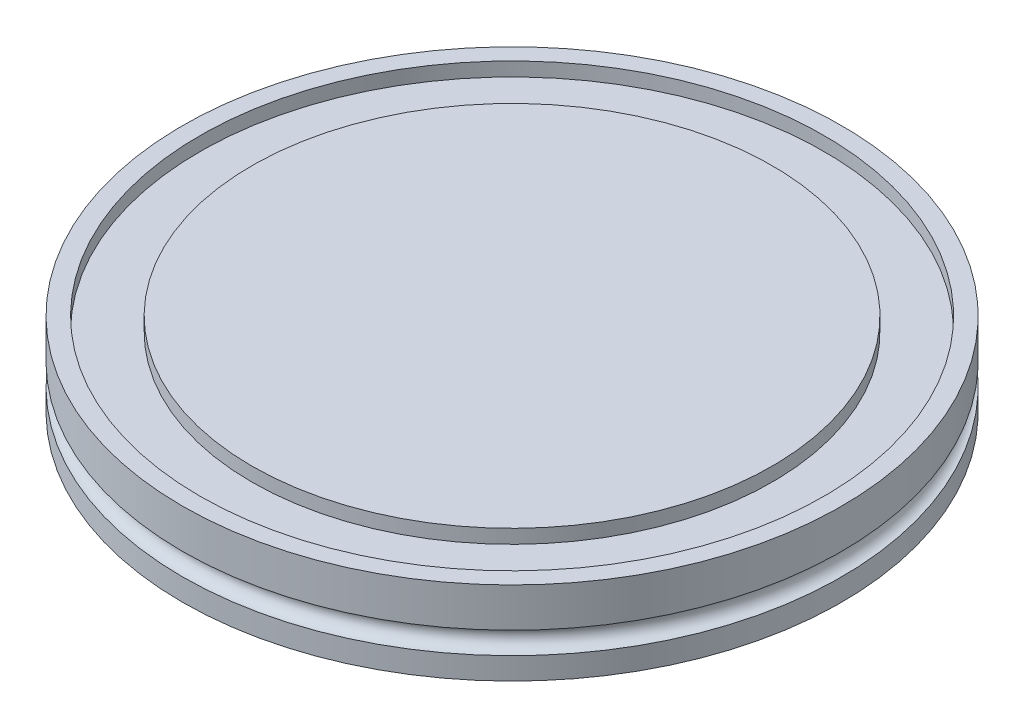
SolidWorks part; units mm, degrees
material "AISI 304"
ref_plane "Front Plane" through (0, 0, 0) normal (0, 0, 1) x (1, 0, 0)
ref_plane "Top Plane" through (0, 0, 0) normal (0, 1, 0) x (1, 0, 0)
ref_plane "Right Plane" through (0, 0, 0) normal (1, 0, 0) x (0, 0, -1)
sketch "Sketch1" plane through (0, 0, 0) normal (0, 0, 1) x (1, 0, 0)
  line L0 (-35, 0) -> (-47.5, 0)
  line L1 (0, 0) -> (-28.65, 0)
  line L2 (0, 0) -> (0, 12)
  line L3 (0, 12) -> (-37.5, 12)
  line L4 (-47.5, 0) -> (-47.5, 3.175)
  line L5 (-45, 12) -> (-47.5, 12)
  line L6 (-35, 0) -> (-35, 3.8)
  line L7 (-35, 3.8) -> (-28.65, 3.8)
  line L8 (-28.65, 0) -> (-28.65, 3.8)
  line L9 (0, 0) -> (0, -4.9927) construction
  line L10 (-45, 12) -> (-45, 10)
  line L11 (-45, 10) -> (-37.5, 10)
  line L12 (-37.5, 12) -> (-37.5, 10)
  line L13 (-47.5, 6.35) -> (-47.5, 12)
  arc A0 (-47.5, 3.175) -> (-47.5, 6.35) centre (-47.5, 4.7625) ccw
  dimension "D1" = 3.175
  dimension "Flange OD" = 95
  dimension "Lip OD" = 90
  dimension "Lip ID" = 75
  dimension "Centering Ring Groove OD" = 70
  dimension "Flange Thickness" = 12
  dimension "D8" = 3.8
  dimension "D9" = 2
  dimension "D10" = 3.175
  dimension "Centering Ring Groove Width" = 6.35
revolve "Revolve1" add sketch "Sketch1" angle 360 about L9
ref_plane "Plane1" through (0, -2, 0) normal (0, -1, 0) x (-1, 0, 0)
